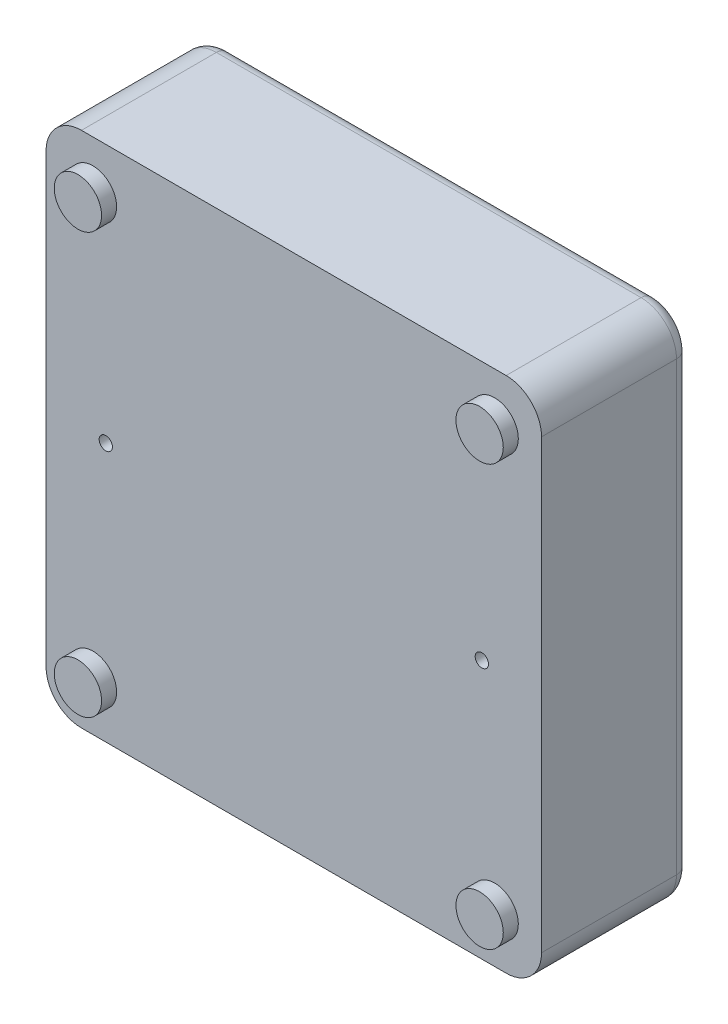
SolidWorks part; units mm, degrees
ref_plane "前视基准面" through (0, 0, 0) normal (0, 0, 1) x (1, 0, 0)
ref_plane "上视基准面" through (0, 0, 0) normal (0, 1, 0) x (1, 0, 0)
ref_plane "右视基准面" through (0, 0, 0) normal (1, 0, 0) x (0, 0, -1)
other "Configuration Table"
sketch "草图1" plane through (0, 0, 0) normal (0, 0, 1) x (1, 0, 0)
  line L1 (-173.8329, 65.1782) -> (-61.8329, 65.1782)
  line L2 (-173.8329, 65.1782) -> (-173.8329, -51.8218)
  line L3 (-173.8329, -51.8218) -> (-61.8329, -51.8218)
  line L4 (-61.8329, 65.1782) -> (-61.8329, -51.8218)
  line L5 (-173.8329, 65.1782) -> (-61.8329, -51.8218) construction
  line L6 (-173.8329, -51.8218) -> (-61.8329, 65.1782) construction
  point P4 (-117.8329, 6.6782)
  dimension "D1" = 112
  dimension "D2" = 117
extrude "凸台-拉伸1" add sketch "草图1" along normal blind 33.5
fillet "圆角1" radius 8 4 edges at (-61.8329, 65.1782, 16.75) (-173.8329, 65.1782, 16.75) (-173.8329, -51.8218, 16.75) (-61.8329, -51.8218, 16.75)
sketch "草图2" plane through (0, 0, 33.5) normal (0, 0, 1) x (1, 0, 0)
  line L0 (-61.8329, 6.6782) -> (-173.8329, 6.6782) construction
  line L1 (-61.8329, -43.8218) -> (-61.8329, 57.1782) construction
  line L2 (-173.8329, 57.1782) -> (-173.8329, -43.8218) construction
  line L3 (-117.8329, -51.8218) -> (-117.8329, 65.1782) construction
  line L4 (-165.8329, -51.8218) -> (-69.8329, -51.8218) construction
  line L5 (-69.8329, 65.1782) -> (-165.8329, 65.1782) construction
  circle A0 centre (-75.3329, 6.6782) radius 1.5
  circle A1 centre (-160.3329, 6.6782) radius 1.5
  dimension "D1" = 3
  dimension "D2" = 85
extrude "切除-拉伸1" cut sketch "草图2" against normal blind 3
sketch "草图3" plane through (0, 0, 33.5) normal (0, 0, 1) x (1, 0, 0)
  line L0 (-61.8329, 6.6782) -> (-173.8329, 6.6782) construction
  line L1 (-61.8329, -43.8218) -> (-61.8329, 57.1782) construction
  line L2 (-173.8329, 57.1782) -> (-173.8329, -43.8218) construction
  line L3 (-117.8329, -51.8218) -> (-117.8329, 65.1782) construction
  line L4 (-165.8329, -51.8218) -> (-69.8329, -51.8218) construction
  line L5 (-69.8329, 65.1782) -> (-165.8329, 65.1782) construction
  circle A0 centre (-72.4329, -40.8218) radius 5.35
  circle A1 centre (-163.2329, -40.8218) radius 5.35
  circle A2 centre (-163.2329, 54.1782) radius 5.35
  circle A3 centre (-72.4329, 54.1782) radius 5.35
  dimension "D1" = 10.7
  dimension "D2" = 95
  dimension "D3" = 90.8
extrude "凸台-拉伸2" add sketch "草图3" along normal blind 3.4
fillet "圆角2" radius 3 8 edges at (-64.1761, -49.4787, 0) (-117.8329, -51.8218, 0) (-171.4898, -49.4787, 0) (-173.8329, 6.6782, 0) (-171.4898, 62.835, 0) (-117.8329, 65.1782, 0) (-64.1761, 62.835, 0) (-61.8329, 6.6782, 0)
